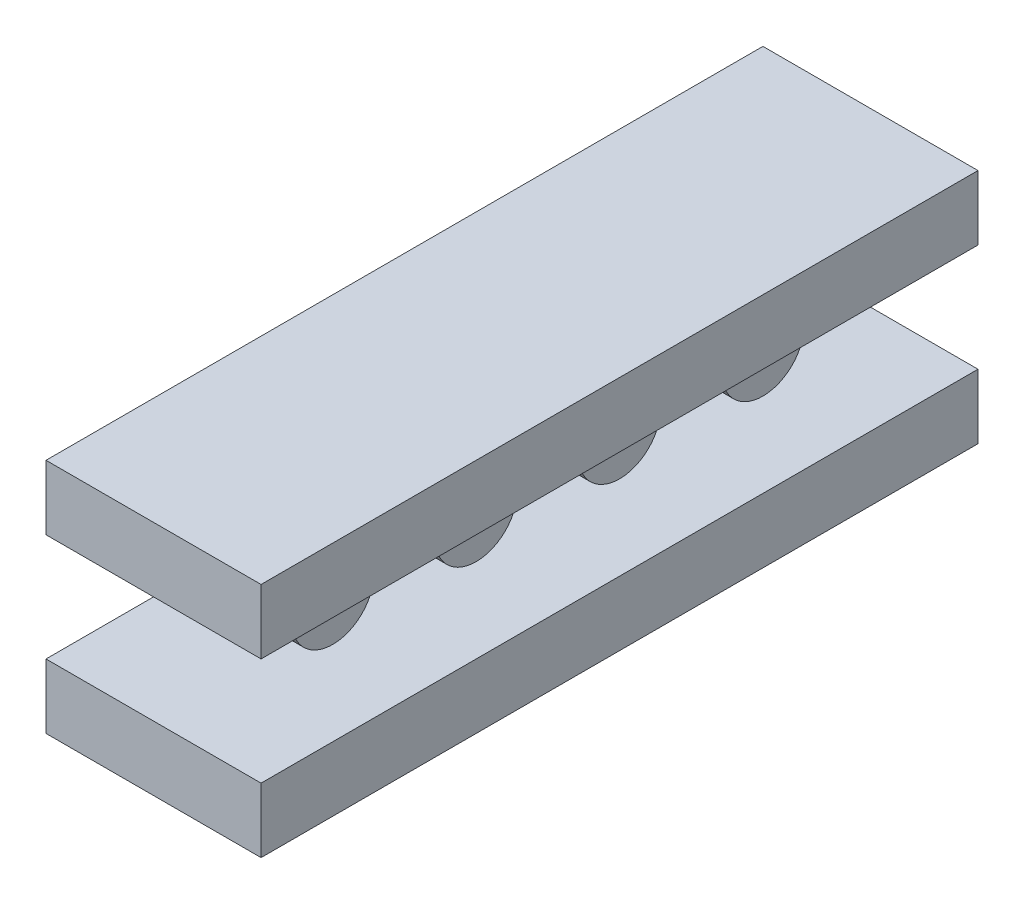
SolidWorks part; units mm, degrees
ref_plane "Front Plane" through (0, 0, 0) normal (0, 0, 1) x (1, 0, 0)
ref_plane "Top Plane" through (0, 0, 0) normal (0, 1, 0) x (1, 0, 0)
ref_plane "Right Plane" through (0, 0, 0) normal (1, 0, 0) x (0, 0, -1)
sketch "Sketch1" plane through (0, 0, 0) normal (1, 0, 0) x (0, 0, -1)
  line L0 (0, 1.2) -> (0, -1.2) construction
  line L2 (5, 0.75) -> (-5, 0.75)
  line L3 (5, 0.75) -> (5, 1.65)
  line L4 (5, 1.65) -> (-5, 1.65)
  line L5 (-5, 0.75) -> (-5, 1.65)
  line L6 (5, 0.75) -> (-5, 1.65) construction
  line L7 (5, 1.65) -> (-5, 0.75) construction
  line L8 (5, -1.65) -> (-5, -1.65)
  line L9 (5, -1.65) -> (5, -0.75)
  line L10 (5, -0.75) -> (-5, -0.75)
  line L11 (-5, -1.65) -> (-5, -0.75)
  line L12 (5, -1.65) -> (-5, -0.75) construction
  line L13 (5, -0.75) -> (-5, -1.65) construction
  point P0 (0, 1.2)
  point P5 (0, -1.2)
  dimension "D1" = 10
  dimension "D2" = 0.9
  dimension "D3" = 1.5
extrude "Boss-Extrude1" add sketch "Sketch1" along normal blind 3
sketch "Sketch2" plane through (0, 0, 0) normal (-1, 0, 0) x (0, 0, 1)
  circle A0 centre (-3, 0) radius 0.575
  circle A1 centre (-1, 0) radius 0.575
  circle A2 centre (1, 0) radius 0.575
  circle A3 centre (3, 0) radius 0.575
  dimension "D1" = 1.15
  dimension "D2" = 1
  dimension "D3" = 2
  dimension "D4" = 1
  dimension "D5" = 2
extrude "Boss-Extrude2" add sketch "Sketch2" against normal blind 2 separate body
